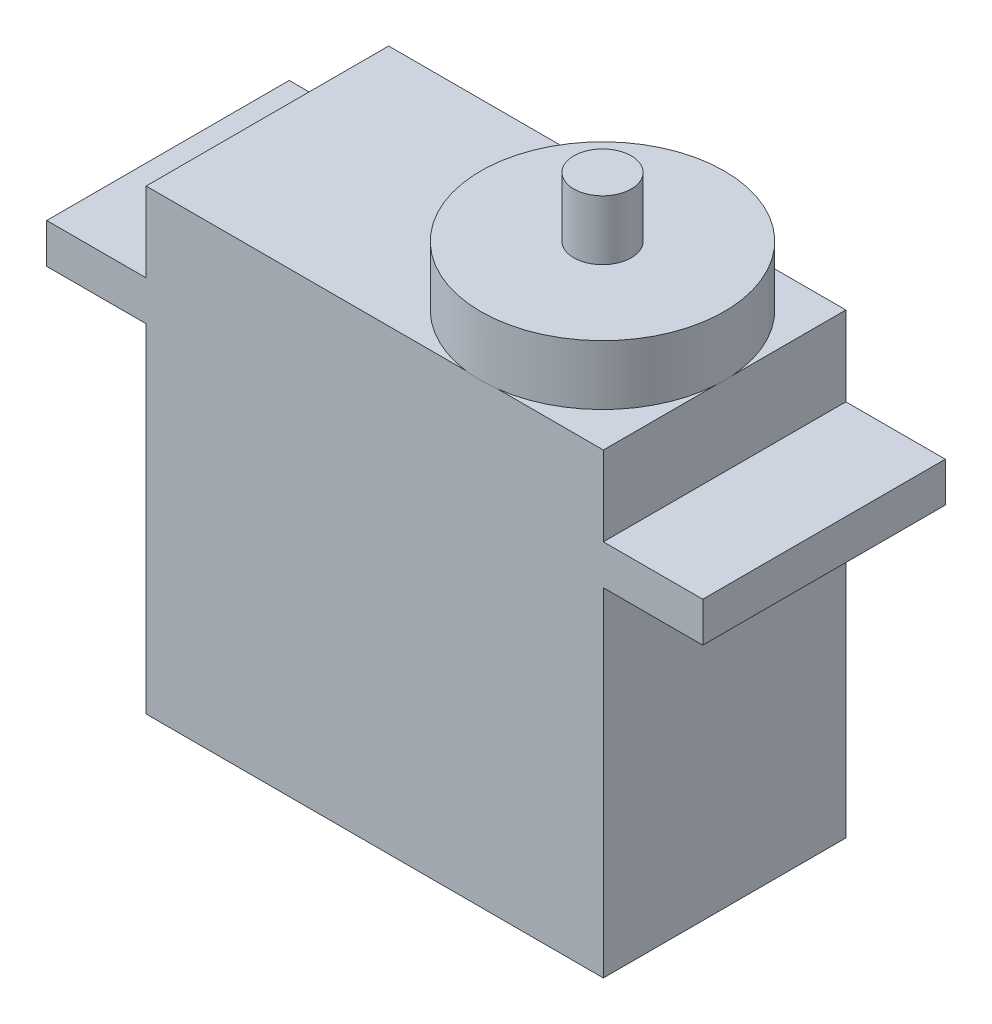
SolidWorks part; units mm, degrees
material "ABS"
ref_plane "Front Plane" through (0, 0, 0) normal (0, 0, 1) x (1, 0, 0)
ref_plane "Top Plane" through (0, 0, 0) normal (0, 1, 0) x (1, 0, 0)
ref_plane "Right Plane" through (0, 0, 0) normal (1, 0, 0) x (0, 0, -1)
sketch "Sketch1" plane through (0, 0, 0) normal (0, 0, 1) x (1, 0, 0)
  line L0 (20.0093, 23) -> (20.0093, 19) construction
  line L1 (0, 0) -> (23, 0)
  line L2 (0, 0) -> (0, 17)
  line L3 (0, 23) -> (23, 23)
  line L4 (23, 0) -> (23, 17)
  line L5 (2.7815, 23) -> (2.7815, 19) construction
  line L6 (23, 19) -> (28, 19)
  line L7 (0, 19) -> (-5, 19)
  line L8 (-5, 19) -> (-5, 17)
  line L9 (28, 19) -> (28, 17)
  line L10 (-5, 17) -> (0, 17)
  line L11 (28, 17) -> (23, 17)
  line L12 (0, 19) -> (0, 23)
  line L13 (23, 19) -> (23, 23)
  dimension "D1" = 23
  dimension "D2" = 23
  dimension "D3" = 4
  dimension "D4" = 5
  dimension "D5" = 2
extrude "Boss-Extrude1" add sketch "Sketch1" along normal blind 12.2
sketch "Sketch2" plane through (0, 23, 0) normal (0, 1, 0) x (1, 0, 0)
  circle A0 centre (16.8845, -6.1264) radius 6.1267
extrude "Boss-Extrude2" add sketch "Sketch2" along normal blind 3
sketch "Sketch3" plane through (0, 26, 0) normal (0, 1, 0) x (1, 0, 0)
  circle A0 centre (16.8845, -6.1264) radius 1.445
  dimension "D1" = 2.89
extrude "Boss-Extrude3" add sketch "Sketch3" along normal blind 3
